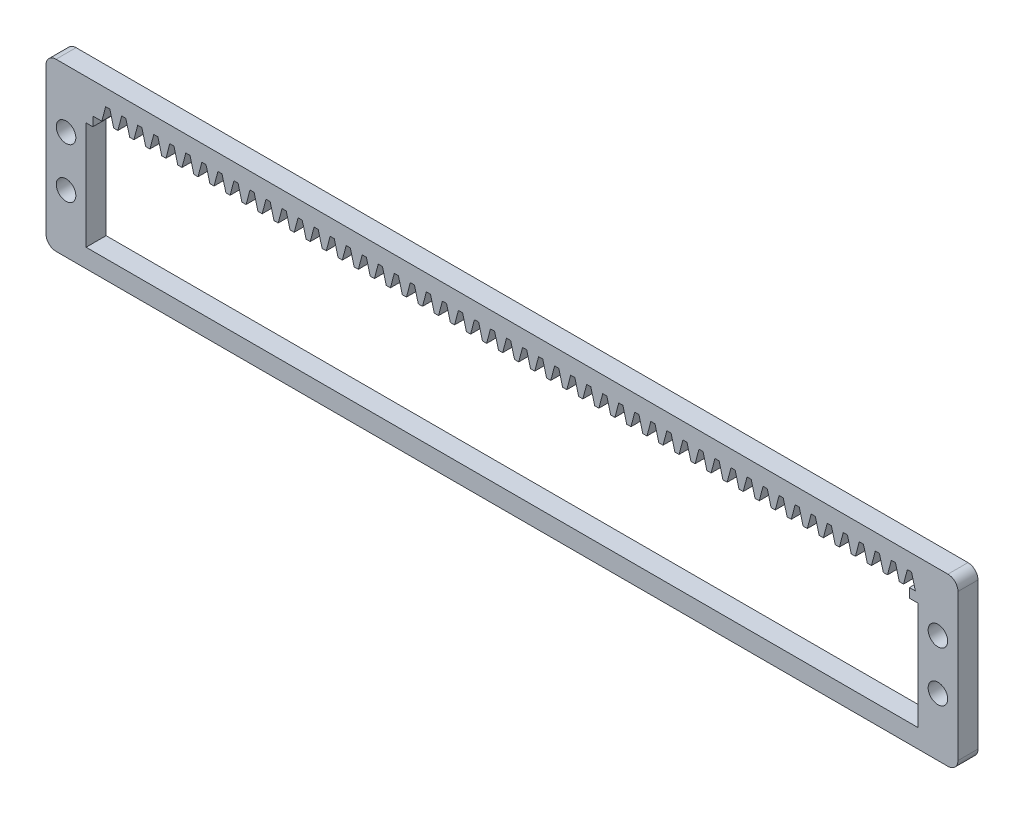
SolidWorks part; units mm, degrees
other "Markup1"
sketch "Sketch6" plane through (0, -30, 3.6) normal (0, 0, 1) x (1, 0, 0)
other "Markup2"
sketch "Sketch7" plane through (0, -30, 3.6) normal (0, 0, 1) x (1, 0, 0)
ref_plane "Front Plane" through (0, 0, 0) normal (0, 0, 1) x (1, 0, 0)
ref_plane "Top Plane" through (0, 0, 0) normal (0, 1, 0) x (1, 0, 0)
ref_plane "Right Plane" through (0, 0, 0) normal (1, 0, 0) x (0, 0, -1)
sketch "Sketch1" plane through (0, 0, 0) normal (0, 0, 1) x (1, 0, 0)
  line L1 (2, 0) -> (180, 0)
  line L2 (0, -2) -> (0, -31.22)
  line L3 (2, -33.22) -> (180, -33.22)
  line L4 (182, -2) -> (182, -31.22)
  arc A0 (180, -33.22) -> (182, -31.22) centre (180, -31.22) ccw
  arc A1 (0, -31.22) -> (2, -33.22) centre (2, -31.22) ccw
  arc A2 (2, 0) -> (0, -2) centre (2, -2) ccw
  arc A3 (180, 0) -> (182, -2) centre (180, -2) cw
  point P7 (182, -33.22)
  point P12 (0, 0)
  point P15 (182, 0)
  dimension "D3" = 2
  dimension "D1" = 33.22
  dimension "D2" = 182
extrude "Boss-Extrude1" add sketch "Sketch1" along normal blind 4
sketch "Sketch2" plane through (0, 0, 4) normal (0, 0, 1) x (1, 0, 0)
  line L0 (2, -33.22) -> (180, -33.22) construction
  line L1 (8, -8) -> (174, -8)
  line L2 (8, -8) -> (8, -29.5)
  line L3 (8, -29.5) -> (174, -29.5)
  line L4 (174, -8) -> (174, -29.5)
  line L5 (0, -2) -> (0, -31.22) construction
  line L7 (182, -31.22) -> (182, -2) construction
  line L8 (8, -18.75) -> (174, -18.75) construction
  line L12 (8, -29.5) -> (174, -29.5) construction
  line L13 (174, -4.3144) -> (174, -29.5) construction
  dimension "D1" = 21.5
  dimension "D2" = 8
  dimension "D3" = 8
  dimension "D4" = 3.72
extrude "Cut-Extrude1" cut sketch "Sketch2" against normal through all
sketch "Sketch3" plane through (0, 0, 4) normal (0, 0, 1) x (1, 0, 0)
  line L0 (174, -8) -> (8, -8) construction
  line L1 (9.35, -8) -> (172.32, -8)
  line L2 (9.35, -8) -> (9.35, -6.15)
  line L3 (9.35, -6.15) -> (172.32, -6.15)
  line L4 (172.32, -8) -> (172.32, -6.15)
  line L5 (174, -29.5) -> (174, -8) construction
  line L6 (8, -8) -> (8, -29.5) construction
  dimension "D1" = 1.85
  dimension "D2" = 1.68
  dimension "D3" = 1.35
extrude "Cut-Extrude2" cut sketch "Sketch3" against normal through all
sketch "Sketch4" plane through (0, 0, 4) normal (0, 0, 1) x (1, 0, 0)
  line L0 (174.7, -6.15) -> (173.5, -6.15) construction
  line L1 (172.32, -6.15) -> (9.35, -6.15) construction
  line L2 (174.7, -6.15) -> (175.465, -3.2492) construction
  line L3 (175.465, -3.2492) -> (172.735, -3.2492) construction
  line L4 (172.735, -3.2492) -> (173.5, -6.15)
  line L5 (172.735, -3.2492) -> (171.905, -3.2492)
  line L6 (171.905, -3.2492) -> (171.14, -6.15)
  line L7 (171.14, -6.15) -> (173.5, -6.15)
  line L10 (173.5, -6.15) -> (174.7, -6.15) construction
  dimension "D1" = 1.2
  dimension "D3" = 3
  dimension "D4" = 0.83
  dimension "D5" = 2.73
extrude "Cut-Extrude4" cut sketch "Sketch4" against normal through all
pattern_linear "LPattern1" count 51 spacing 3.2 along (-1, 0, 0) of "Cut-Extrude4"
sketch "Sketch5" plane through (0, 0, 4) normal (0, 0, 1) x (1, 0, 0)
  line L0 (174, -16.61) -> (182, -16.61) construction
  line L1 (180, 0) -> (2, 0) construction
  line L2 (8, -8) -> (8, -29.5) construction
  line L3 (0, -2) -> (0, -31.22) construction
  line L4 (2, -33.22) -> (180, -33.22) construction
  line L5 (0, -16.61) -> (8, -16.61) construction
  line L7 (178, -11.61) -> (178, -21.61) construction
  line L8 (4, -11.61) -> (4, -21.61) construction
  line L9 (174, -29.5) -> (174, -8) construction
  line L10 (182, -31.22) -> (182, -2) construction
  circle A4 centre (4, -11.61) radius 1.95
  circle A5 centre (4, -21.61) radius 1.95
  circle A6 centre (178, -11.61) radius 1.95
  circle A7 centre (178, -21.61) radius 1.95
  point P8 (178, -16.61)
  point P18 (4, -16.61)
  point P22 (4, -16.61)
  point P31 (178, -16.61)
  dimension "D1" = 3.9
  dimension "D3" = 3.9
  dimension "D4" = 3.9
  dimension "D6" = 3.9
  dimension "D5" = 10
  dimension "D7" = 10
extrude "Cut-Extrude5" cut sketch "Sketch5" against normal blind 10
